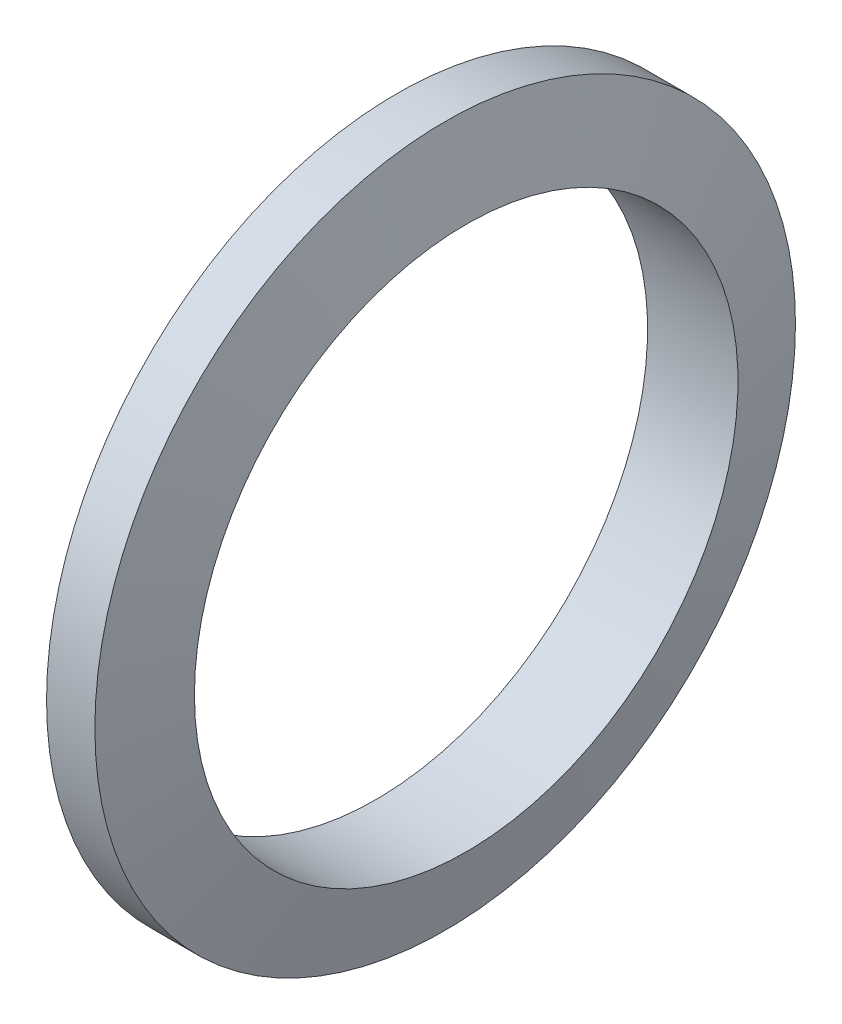
SolidWorks part; units mm, degrees
ref_plane "Спереди" through (0, 0, 0) normal (0, 0, 1) x (1, 0, 0)
ref_plane "Сверху" through (0, 0, 0) normal (0, 1, 0) x (1, 0, 0)
ref_plane "Справа" through (0, 0, 0) normal (1, 0, 0) x (0, 0, -1)
sketch "Ske" plane through (0, 0, 0) normal (0, 0, 1) x (1, 0, 0)
  line L0 (-10, 0) -> (10, 0) construction
  line L1 (0, 0) -> (0, 29) construction
  line L2 (-2, 29) -> (2, 29)
  line L3 (2, 29) -> (3.7417, 22.5)
  line L4 (-3.7417, 22.5) -> (3.7417, 22.5)
  line L5 (-2, 29) -> (-3.7417, 22.5)
  dimension "D1" = 58
  dimension "d" = 45
  dimension "b2" = 4
  dimension "D4" = 30
revolve "Основание-Повернуть" add sketch "Ske" angle 360 about L0
